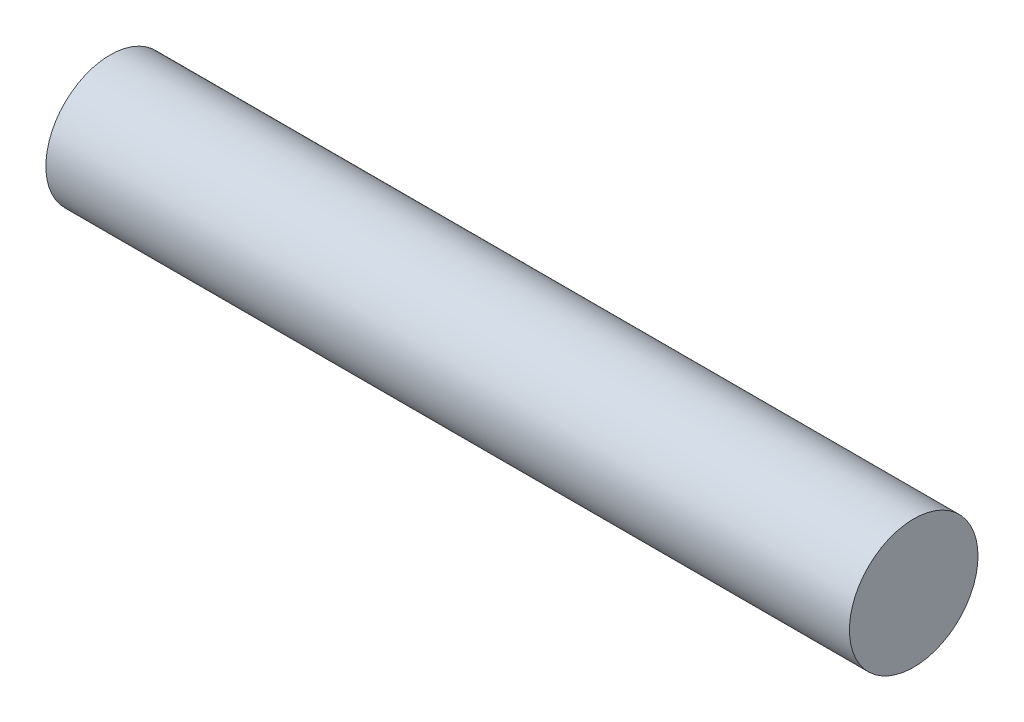
SolidWorks part; units mm, degrees
material "6061-T6 (SS)"
ref_plane "Front Plane" through (0, 0, 0) normal (0, 0, 1) x (1, 0, 0)
ref_plane "Top Plane" through (0, 0, 0) normal (0, 1, 0) x (1, 0, 0)
ref_plane "Right Plane" through (0, 0, 0) normal (1, 0, 0) x (0, 0, -1)
sketch "Sketch1" plane through (0, 0, 0) normal (1, 0, 0) x (0, 0, -1)
  circle A0 centre (0, 0) radius 12.7
  dimension "D1" = 25.4
extrude "Boss-Extrude1" add sketch "Sketch1" along normal blind 158.75
